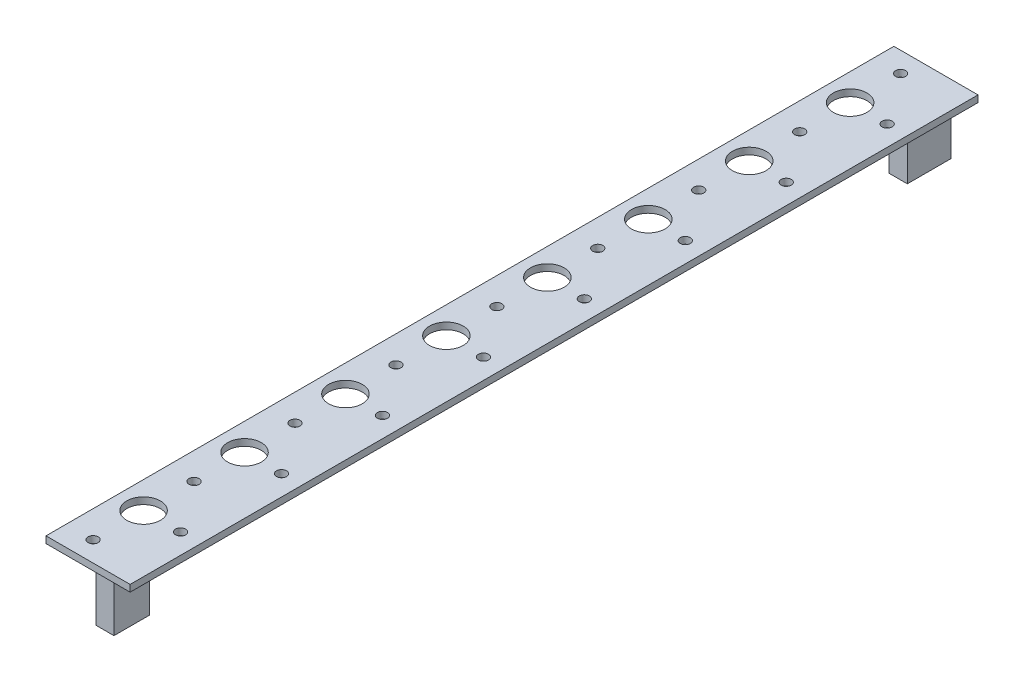
SolidWorks part; units mm, degrees
material "Cuivre"
ref_plane "Plan de face" through (0, 0, 0) normal (0, 0, 1) x (1, 0, 0)
ref_plane "Plan de dessus" through (0, 0, 0) normal (0, 1, 0) x (1, 0, 0)
ref_plane "Plan de droite" through (0, 0, 0) normal (1, 0, 0) x (0, 0, -1)
sketch "Esquisse1" plane through (0, 0, 0) normal (0, 1, 0) x (1, 0, 0)
  line L0 (-4.5, 105) -> (-4.5, 75) construction
  line L1 (-12.5, -126) -> (12.5, -126)
  line L2 (-12.5, -126) -> (-12.5, 126)
  line L3 (-12.5, 126) -> (12.5, 126)
  line L4 (12.5, -126) -> (12.5, 126)
  line L5 (-12.5, -126) -> (12.5, 126) construction
  line L6 (-12.5, 126) -> (12.5, -126) construction
  line L7 (-4.5, 120) -> (-4.5, 90) construction
  circle A0 centre (-4.5, 105) radius 5
  circle A1 centre (6.5, 105) radius 1.5
  circle A2 centre (-4.5, 75) radius 5
  circle A3 centre (6.5, 75) radius 1.5
  circle A4 centre (-4.5, 45) radius 5
  circle A5 centre (6.5, 45) radius 1.5
  circle A6 centre (-4.5, 15) radius 5
  circle A7 centre (6.5, 15) radius 1.5
  circle A8 centre (-4.5, -15) radius 5
  circle A9 centre (6.5, -15) radius 1.5
  circle A10 centre (-4.5, -45) radius 5
  circle A11 centre (6.5, -45) radius 1.5
  circle A12 centre (-4.5, -75) radius 5
  circle A13 centre (6.5, -75) radius 1.5
  circle A14 centre (-4.5, -105) radius 5
  circle A15 centre (6.5, -105) radius 1.5
  circle A16 centre (-4.5, 120) radius 1.5
  circle A17 centre (-4.5, 90) radius 1.5
  circle A18 centre (-4.5, 60) radius 1.5
  circle A19 centre (-4.5, 30) radius 1.5
  circle A20 centre (-4.5, 0) radius 1.5
  circle A21 centre (-4.5, -30) radius 1.5
  circle A22 centre (-4.5, -60) radius 1.5
  circle A23 centre (-4.5, -90) radius 1.5
  circle A24 centre (-4.5, -120) radius 1.5
  point P0 (0, 0)
  dimension "D5" = 10
  dimension "D6" = 3
  dimension "D10" = 3
  dimension "D1" = 25
  dimension "D2" = 252
  dimension "D3" = 21
  dimension "D4" = 17
  dimension "D7" = 11
  dimension "D9" = 30
  dimension "D11" = 15
  dimension "D13" = 30
  dimension "D8" = 8
  dimension "D12" = 9
extrude "Boss.-Extru.1" add sketch "Esquisse1" along normal blind 2
sketch "Esquisse2" plane through (0, 0, 0) normal (0, -1, 0) x (1, 0, 0)
  line L0 (12.5, -126) -> (-12.5, -126) construction
  line L1 (6.9, -123.6) -> (1.5, -123.6)
  line L2 (6.9, -123.6) -> (6.9, -110.6)
  line L3 (6.9, -110.6) -> (1.5, -110.6)
  line L4 (1.5, -123.6) -> (1.5, -110.6)
  line L5 (-0.1, 113) -> (5.3, 113)
  line L6 (-0.1, 113) -> (-0.1, 123.6)
  line L7 (-0.1, 123.6) -> (5.3, 123.6)
  line L8 (5.3, 113) -> (5.3, 123.6)
  line L9 (12.5, 126) -> (12.5, -126) construction
  line L10 (-12.5, 126) -> (12.5, 126) construction
  point P8 (4.2, -123.6)
  point P13 (2.6, 123.6)
  dimension "D1" = 5.4
  dimension "D2" = 13
  dimension "D3" = 2.4
  dimension "D4" = 5.6
  dimension "D5" = 5.4
  dimension "D6" = 10.6
  dimension "D7" = 2.4
  dimension "D8" = 7.2
extrude "Boss.-Extru.2" add sketch "Esquisse2" along normal blind 16
